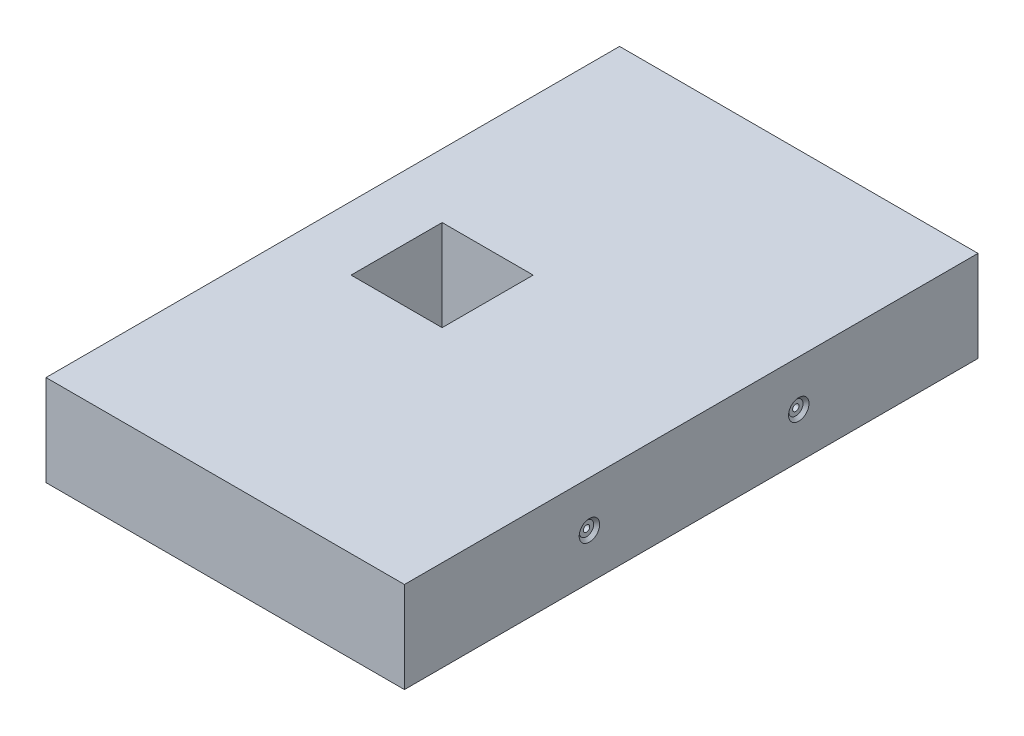
SolidWorks part; units mm, degrees
ref_plane "Front Plane" through (0, 0, 0) normal (0, 0, 1) x (1, 0, 0)
ref_plane "Top Plane" through (0, 0, 0) normal (0, 1, 0) x (1, 0, 0)
ref_plane "Right Plane" through (0, 0, 0) normal (1, 0, 0) x (0, 0, -1)
sketch "Sketch1" plane through (0, 0, 0) normal (0, 1, 0) x (1, 0, 0)
  line L1 (-50, 80) -> (50, 80)
  line L2 (-50, 80) -> (-50, -80)
  line L3 (-50, -80) -> (50, -80)
  line L4 (50, 80) -> (50, -80)
  line L5 (-50, 80) -> (50, -80) construction
  line L6 (-50, -80) -> (50, 80) construction
  line L7 (-32.19, 12.7) -> (-6.79, 12.7)
  line L8 (-32.19, 12.7) -> (-32.19, -12.7)
  line L9 (-32.19, -12.7) -> (-6.79, -12.7)
  line L10 (-6.79, 12.7) -> (-6.79, -12.7)
  line L11 (-32.19, 12.7) -> (-6.79, -12.7) construction
  line L12 (-32.19, -12.7) -> (-6.79, 12.7) construction
  point P0 (0, 0)
  point P6 (0, 0)
  dimension "D1" = 100
  dimension "D2" = 160
  dimension "D3" = 25.4
  dimension "D4" = 25.4
  dimension "D5" = 56.79
extrude "Boss-Extrude1" add sketch "Sketch1" along normal blind 25.4
hole_wizard "CBORE for #0 Binding Head Machine Screw1" positions "Sketch2" profile "Sketch3" counterbore size "#0" standard "ANSI Inch"
sketch "Sketch2" plane through (50, 0, 0) normal (1, 0, 0) x (0, 0, -1)
  line L0 (-80, 0) -> (80, 0) construction
  line L2 (80, 25.4) -> (80, 0) construction
  point P0 (-28.4, 12.7)
  point P2 (30, 12.7)
  dimension "D1" = 12.7
  dimension "D2" = 58.4
  dimension "D3" = 50
sketch "Sketch3" plane through (50, 12.7, 28.4) normal (0, 1, 0) x (0, 0, -1)
  line L0 (0, 0) -> (0, 30.5342)
  line L1 (0, 30.5342) -> (0.889, 30)
  line L2 (0.889, 30) -> (0.889, 0.8128)
  line L3 (0.889, 0.8128) -> (1.985, 0.8128)
  line L5 (1.985, 0.8128) -> (1.985, 0.8725)
  line L6 (1.985, 0.8725) -> (2.8575, 0)
  line L7 (2.8575, 0) -> (0, 0)
  line L8 (-1.985, 0.8725) -> (-2.8575, 0) construction
  line L10 (0, 30.5342) -> (-0.889, 30) construction
  line L11 (0, -6.35) -> (0, 107.95) construction
  dimension "Hole Dia." = 1.778
  dimension "Hole Depth" = 30
  dimension "C'Bore Dia." = 3.97
  dimension "C'Bore Depth" = 0.8128
  dimension "Near C'Sink Dia." = 5.715
  dimension "Near C'Sink Angle" = 90
  dimension "Drill Angle" = 118
